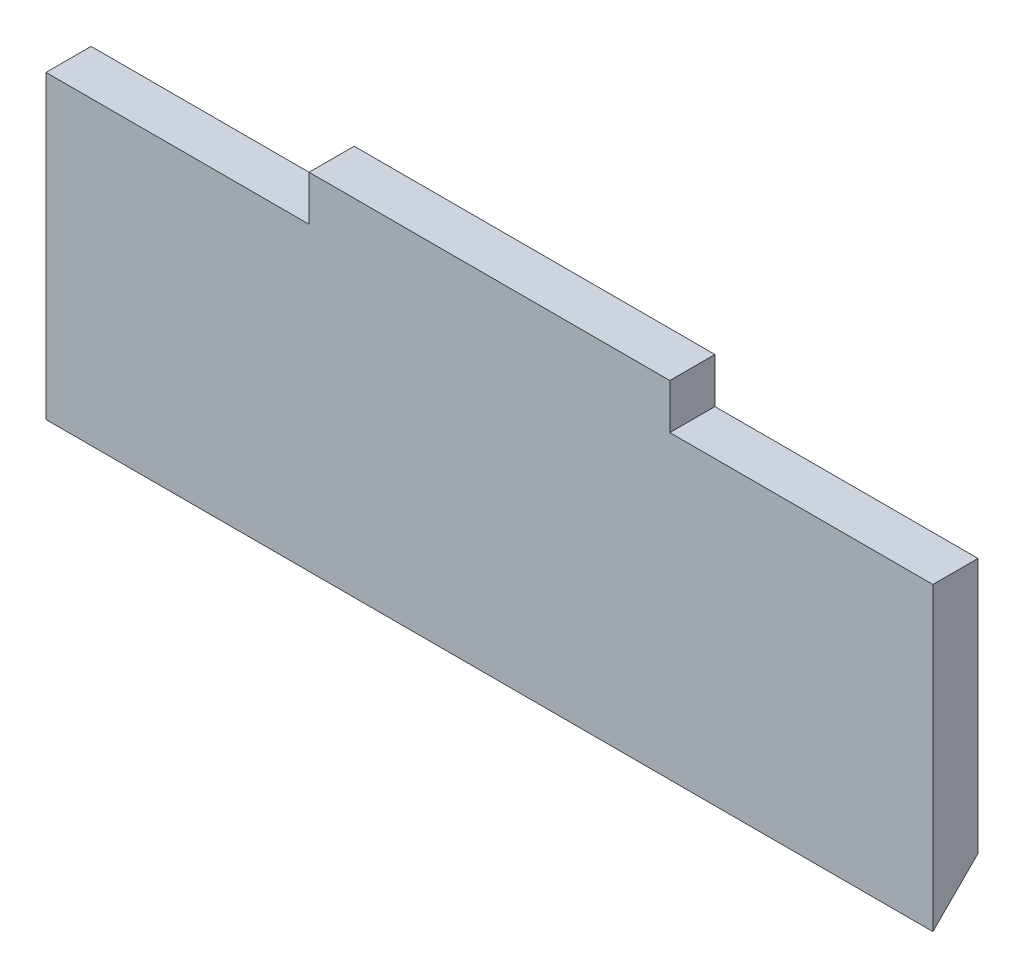
SolidWorks part; units mm, degrees
ref_plane "Plan de face" through (0, 0, 0) normal (0, 0, 1) x (1, 0, 0)
ref_plane "Plan de dessus" through (0, 0, 0) normal (0, 1, 0) x (1, 0, 0)
ref_plane "Plan de droite" through (0, 0, 0) normal (1, 0, 0) x (0, 0, -1)
sketch "Esquisse1" plane through (0, 0, 0) normal (0, 0, 1) x (1, 0, 0)
  line L1 (60, 20) -> (-60, 20)
  line L2 (60, 20) -> (60, -20)
  line L3 (60, -20) -> (-60, -20)
  line L4 (-60, 20) -> (-60, -20)
  line L5 (60, 20) -> (-60, -20) construction
  line L6 (60, -20) -> (-60, 20) construction
  point P0 (0, 0)
  dimension "D1" = 120
  dimension "D2" = 40
extrude "Boss.-Extru.1" add sketch "Esquisse1" along normal blind 6
sketch "Esquisse2" plane through (0, 0, 6) normal (0, 0, 1) x (1, 0, 0)
  line L0 (60, 20) -> (-60, 20) construction
  line L1 (-25, 20) -> (25, 20)
  line L2 (-25, 20) -> (-25, 26)
  line L3 (-25, 26) -> (25, 26)
  line L4 (25, 20) -> (25, 26)
  line L5 (-60, 20) -> (-60, -20) construction
  line L6 (60, -20) -> (60, 20) construction
  line L7 (-60, 0) -> (60, 0) construction
  dimension "D1" = 50
  dimension "D2" = 35
  dimension "D3" = 6
extrude "Boss.-Extru.2" add sketch "Esquisse2" against normal blind 6
sketch "Sketch1" plane through (-60, 0, 0) normal (-1, 0, 0) x (0, 0, 1)
  line L0 (6, -20) -> (0, -14)
  line L1 (0, 20) -> (0, -20) construction
  line L2 (0, -14) -> (0, -20)
  line L4 (0, -20) -> (6, -20)
extrude "Cut-Extrude1" cut sketch "Sketch1" against normal blind 40
sketch "Sketch2" plane through (60, 0, 0) normal (1, 0, 0) x (0, 0, -1)
  line L0 (-6, -20) -> (0, -14)
  line L1 (0, -20) -> (0, 20) construction
  line L2 (0, -14) -> (0, -20)
  line L3 (0, -20) -> (-6, -20)
extrude "Cut-Extrude2" cut sketch "Sketch2" against normal blind 40
sketch "Sketch3" plane through (0, 0, 6) normal (0, 0, 1) x (1, 0, 0)
  line L0 (20, -20) -> (60, -20) construction
  line L1 (60, -20) -> (59, -20)
  line L2 (60, -20) -> (60, 20)
  line L3 (60, 20) -> (59, 20)
  line L4 (59, -20) -> (59, 20)
  line L5 (60, -20) -> (60, 20) construction
  line L6 (60, 20) -> (25, 20) construction
  line L7 (25, 26) -> (-25, 26) construction
  line L8 (25, 20) -> (24, 20)
  line L9 (25, 20) -> (25, 26)
  line L10 (25, 26) -> (24, 26)
  line L11 (24, 20) -> (24, 26)
  line L12 (-25, 20) -> (-60, 20) construction
  line L13 (-25, 20) -> (-24, 20)
  line L14 (-25, 20) -> (-25, 26)
  line L15 (-25, 26) -> (-24, 26)
  line L16 (-24, 20) -> (-24, 26)
  line L17 (-60, -20) -> (-59, -20)
  line L18 (-60, -20) -> (-60, 20)
  line L19 (-60, 20) -> (-59, 20)
  line L20 (-59, -20) -> (-59, 20)
  dimension "D1" = 1
  dimension "D2" = 1
  dimension "D3" = 1
  dimension "D4" = 1
extrude "Cut-Extrude3" cut sketch "Sketch3" against normal through all
